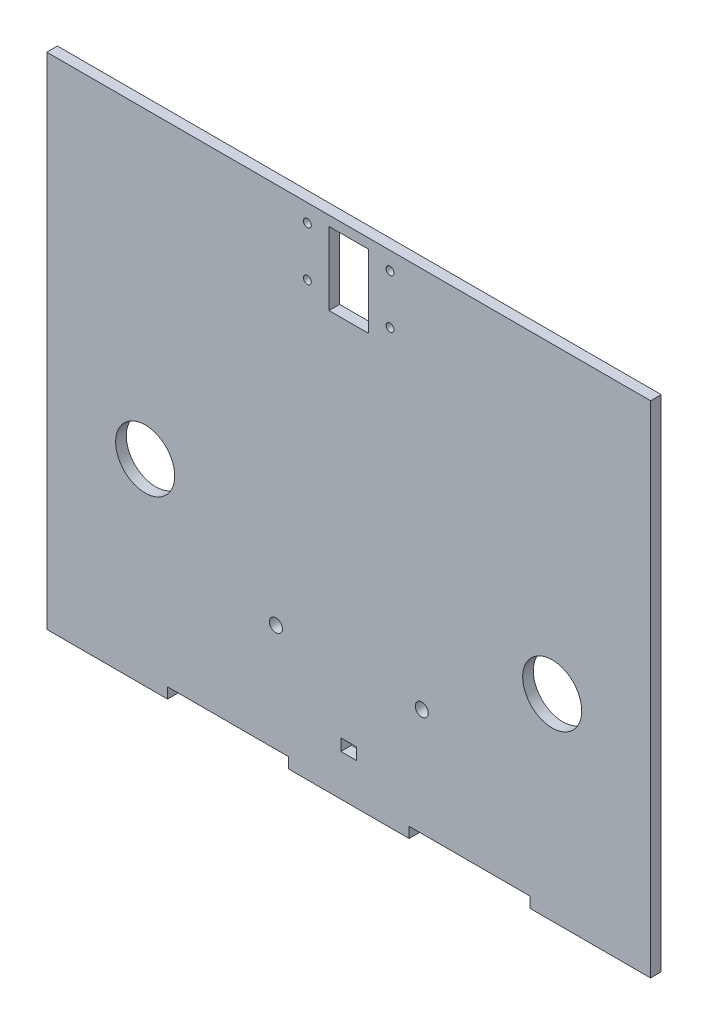
SolidWorks part; units mm, degrees
ref_plane "Ön Düzlem" through (0, 0, 0) normal (0, 0, 1) x (1, 0, 0)
ref_plane "Üst Düzlem" through (0, 0, 0) normal (0, 1, 0) x (1, 0, 0)
ref_plane "Sağ Düzlem" through (0, 0, 0) normal (1, 0, 0) x (0, 0, -1)
sketch "Sketch1" plane through (0, 0, 0) normal (0, 0, 1) x (1, 0, 0)
  line L9 (-2, -17.5) -> (-2, -14.5)
  line L10 (-2, -14.5) -> (2, -14.5)
  line L11 (2, -14.5) -> (2, -17.5)
  line L12 (2, -17.5) -> (-2, -17.5)
  line L21 (-46.02, -28) -> (-46.02, -25.3)
  line L22 (-15.34, -28) -> (-15.34, -25.3)
  line L23 (15.34, -28) -> (15.34, -25.3)
  line L24 (46.02, -28) -> (46.02, -25.3)
  line L33 (-46.02, -28) -> (-76.7, -28)
  line L35 (-15.34, -25.3) -> (-46.02, -25.3)
  line L36 (-15.34, -28) -> (15.34, -28)
  line L37 (15.34, -25.3) -> (46.02, -25.3)
  line L38 (46.02, -28) -> (76.7, -28)
  line L57 (5, 96.5) -> (-5, 96.5)
  line L60 (5, 78) -> (-5, 78)
  line L63 (-5, 78) -> (-5, 96.5)
  line L66 (5, 78) -> (5, 96.5)
  line L67 (76.7, 99) -> (-76.7, 99)
  line L68 (-76.7, -28) -> (-76.7, 99)
  line L69 (76.7, -28) -> (76.7, 99)
  circle A1 centre (-18.5, 2) radius 1.65
  circle A2 centre (18.5679, 2) radius 1.65
  circle A3 centre (-51.7, 22) radius 7.5
  circle A4 centre (51.7, 22) radius 7.5
  circle A9 centre (10.5, 94.5) radius 1
  circle A10 centre (-10.5, 82) radius 1
  circle A11 centre (-10.5, 94.5) radius 1
  circle A12 centre (10.5, 82) radius 1
  point P0 (0, 0)
  point P59 (0, 84.5)
extrude "Boss-Extrude3" add sketch "Sketch1" along normal blind 2.7
